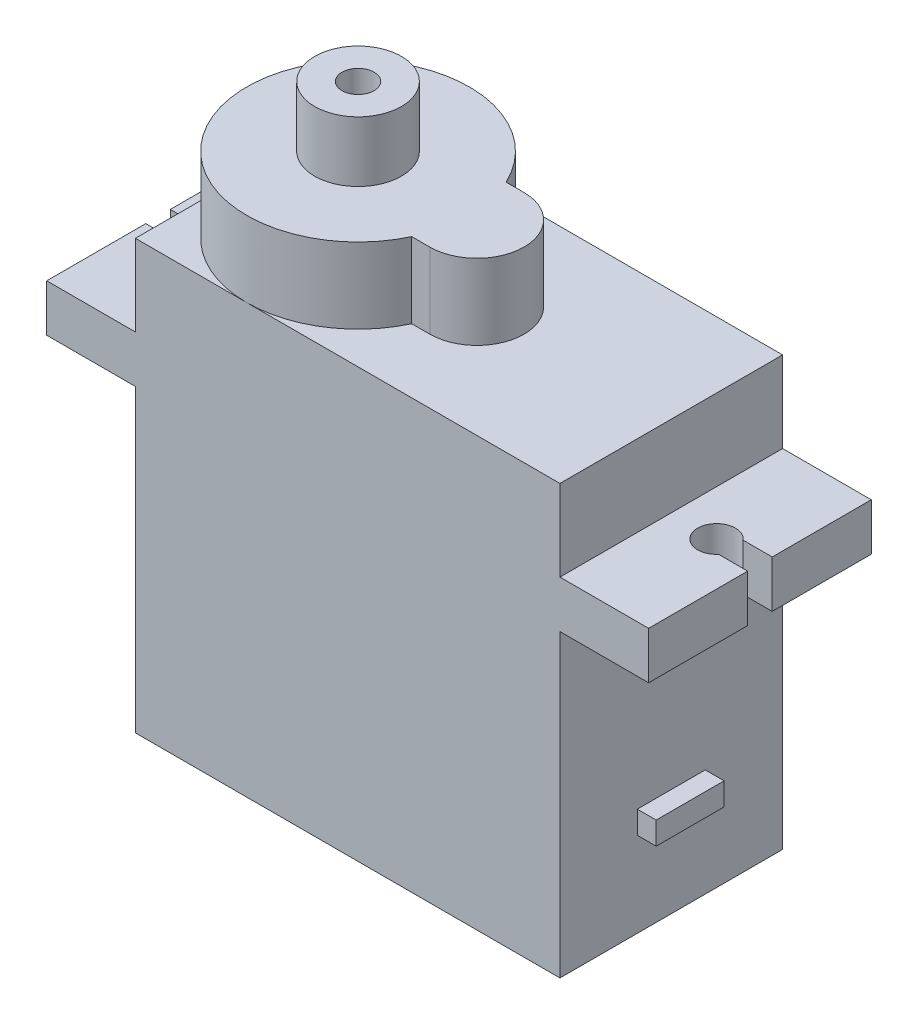
SolidWorks part; units mm, degrees
ref_plane "Front Plane" through (0, 0, 0) normal (0, 0, 1) x (1, 0, 0)
ref_plane "Top Plane" through (0, 0, 0) normal (0, 1, 0) x (1, 0, 0)
ref_plane "Right Plane" through (0, 0, 0) normal (1, 0, 0) x (0, 0, -1)
sketch "Sketch1" plane through (0, 0, 0) normal (0, 1, 0) x (1, 0, 0)
  line L1 (-11.25, -5.9) -> (11.25, -5.9)
  line L2 (-11.25, -5.9) -> (-11.25, 5.9)
  line L3 (-11.25, 5.9) -> (11.25, 5.9)
  line L4 (11.25, -5.9) -> (11.25, 5.9)
  line L5 (0, 5.9) -> (0, -5.9) construction
  line L6 (-11.25, 0) -> (11.25, 0) construction
  point P0 (0, 0)
  dimension "D1" = 11.8
  dimension "D2" = 22.5
extrude "Boss-Extrude1" add sketch "Sketch1" along normal blind 22.7
sketch "Sketch2" plane through (0, 0, 0) normal (0, 1, 0) x (1, 0, 0)
  line L0 (-11.25, -5.9) -> (11.25, -5.9) construction
  line L1 (11.25, 5.9) -> (15.95, 5.9)
  line L2 (11.25, 5.9) -> (11.25, -5.9)
  line L3 (11.25, -5.9) -> (15.95, -5.9)
  line L4 (15.95, 5.9) -> (15.95, -5.9)
  line L5 (13.6, -5.9) -> (13.6, 5.9) construction
  line L6 (11.25, 0) -> (15.95, 0) construction
  line L7 (16.3243, -0.65) -> (13.6, -0.65)
  line L8 (16.3243, -0.65) -> (16.3243, 0.65)
  line L9 (13.6, -0.65) -> (13.6, 0.65)
  line L10 (16.3243, 0.65) -> (13.6, 0.65)
  line L11 (13.6, 0) -> (16.3243, 0) construction
  line L12 (14.9622, -0.65) -> (14.9622, 0.65) construction
  circle A0 centre (13.65, 0) radius 1
  point P9 (14.9622, 0)
  point P156 (13.6, 0)
  dimension "D2" = 2
  dimension "D3" = 2.3
  dimension "D1" = 4.7
  dimension "D4" = 1.3
extrude "Boss-Extrude2" add sketch "Sketch2" along normal blind 2.5 from offset 15.9 contours A0 L10 L4 L1 L2 L3 L7
mirror "Mirror1" about plane through (0, 0, 0) normal (1, 0, 0) of "Boss-Extrude2"
sketch "Sketch3" plane through (0, 22.7, 0) normal (0, 1, 0) x (1, 0, 0)
  line L0 (-11.25, 0) -> (11.25, 0) construction
  line L1 (-11.25, 5.9) -> (-11.25, -5.9) construction
  line L2 (11.25, -5.9) -> (11.25, 5.9) construction
  line L5 (0.95, 2.5) -> (-0.0058, 2.5)
  line L6 (0.95, -2.5) -> (-0.0058, -2.5)
  circle A0 centre (-5.35, 0) radius 5.9
  circle A1 centre (0.95, 0) radius 2.5
  dimension "D1" = 11.8
  dimension "D2" = 5
  dimension "D3" = 12.2
extrude "Boss-Extrude3" add sketch "Sketch3" along normal blind 4 contours A1 A0 L6 | A1 L5 A0 | A0 L0 A1 | A1 L0 A0 | L0 A1 A0 | L0 A0 A1 | L0 A0 A1 | A0 L0 A1
sketch "Sketch4" plane through (0, 26.7, 0) normal (0, 1, 0) x (1, 0, 0)
  circle A0 centre (-5.35, 0) radius 2.3
  circle A1 centre (-5.35, 0) radius 0.85
  dimension "D1" = 4.6
  dimension "D2" = 1.7
extrude "Boss-Extrude4" add sketch "Sketch4" along normal blind 3.2
sketch "Sketch5" plane through (11.25, 0, 0) normal (1, 0, 0) x (0, 0, -1)
  line L0 (0, 0) -> (0, 15.9) construction
  line L2 (-5.9, 0) -> (5.9, 0) construction
  line L3 (-1.8, 4.5) -> (1.8, 4.5)
  line L4 (-1.8, 4.5) -> (-1.8, 5.7)
  line L5 (-1.8, 5.7) -> (1.8, 5.7)
  line L6 (1.8, 4.5) -> (1.8, 5.7)
  line L7 (0, 5.7) -> (0, 4.5) construction
  line L8 (-1.8, 5.1) -> (1.8, 5.1) construction
  point P5 (0, 5.1)
  dimension "D1" = 3.6
  dimension "D2" = 1.2
  dimension "D3" = 4.5
extrude "Boss-Extrude5" add sketch "Sketch5" along normal blind 1
